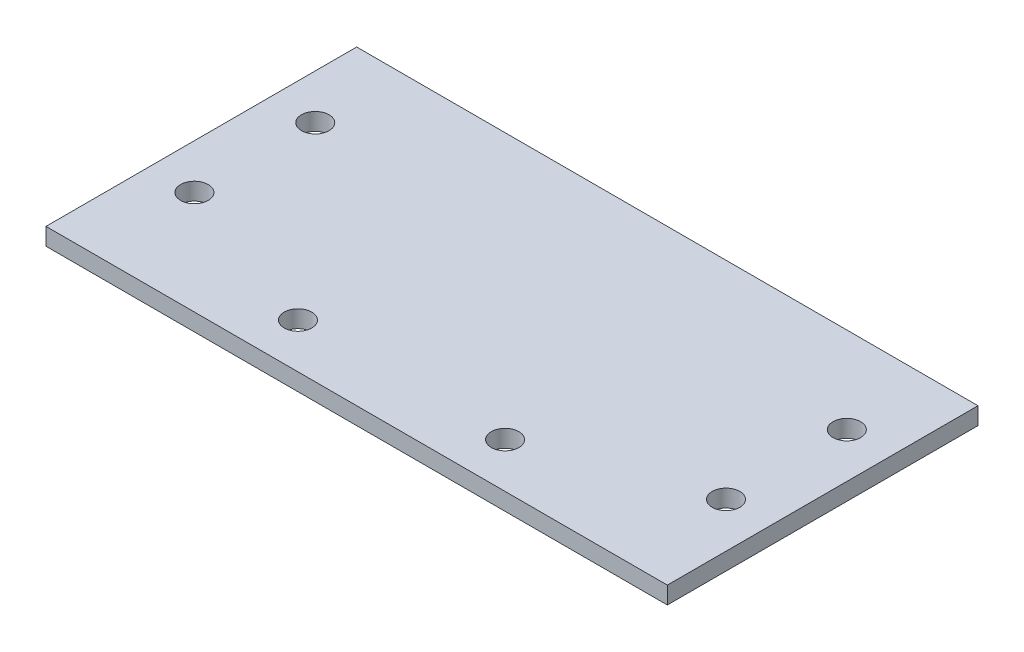
SolidWorks part; units mm, degrees
ref_plane "Front Plane" through (0, 0, 0) normal (0, 0, 1) x (1, 0, 0)
ref_plane "Top Plane" through (0, 0, 0) normal (0, 1, 0) x (1, 0, 0)
ref_plane "Right Plane" through (0, 0, 0) normal (1, 0, 0) x (0, 0, -1)
sketch "Sketch1" plane through (0, 0, 0) normal (0, 1, 0) x (1, 0, 0)
  line L1 (-90, 45) -> (90, 45)
  line L2 (-90, 45) -> (-90, -45)
  line L3 (-90, -45) -> (90, -45)
  line L4 (90, 45) -> (90, -45)
  dimension "D1" = 90
  dimension "D2" = 180
  dimension "D3" = 45
  dimension "D4" = 90
extrude "Boss-Extrude1" add sketch "Sketch1" along normal blind 5
sketch "Sketch2" plane through (0, 5, 0) normal (0, 1, 0) x (1, 0, 0)
  line L0 (-90, -45) -> (90, -45) construction
  line L1 (-90, 45) -> (-90, -45) construction
  point P0 (-77, 20)
  point P2 (-77, -15)
  point P4 (-30, -32)
  point P6 (30, -32)
  point P8 (77, -15)
  point P10 (77, 20)
  dimension "D1" = 35
  dimension "D2" = 30
  dimension "D3" = 13
  dimension "D4" = 60
  dimension "D5" = 107
  dimension "D6" = 154
  dimension "D7" = 13
hole_wizard "Ø1.0mm Dowel Hole1" positions "Sketch2" profile "Sketch3" hole size "Ø1.0" standard "ISO" end condition through all
sketch "Sketch3" plane through (-77, 5, -20) normal (1, 0, 0) x (0, 0, 1)
  line L0 (0, 0) -> (0, 5)
  line L1 (0, 5) -> (4, 5)
  line L2 (4, 5) -> (4, 0)
  line L5 (4, 0) -> (0, 0)
  line L11 (0, -6.35) -> (0, 107.95) construction
  dimension "Thru Hole Dia." = 8
  dimension "Thru Hole Depth" = 5
